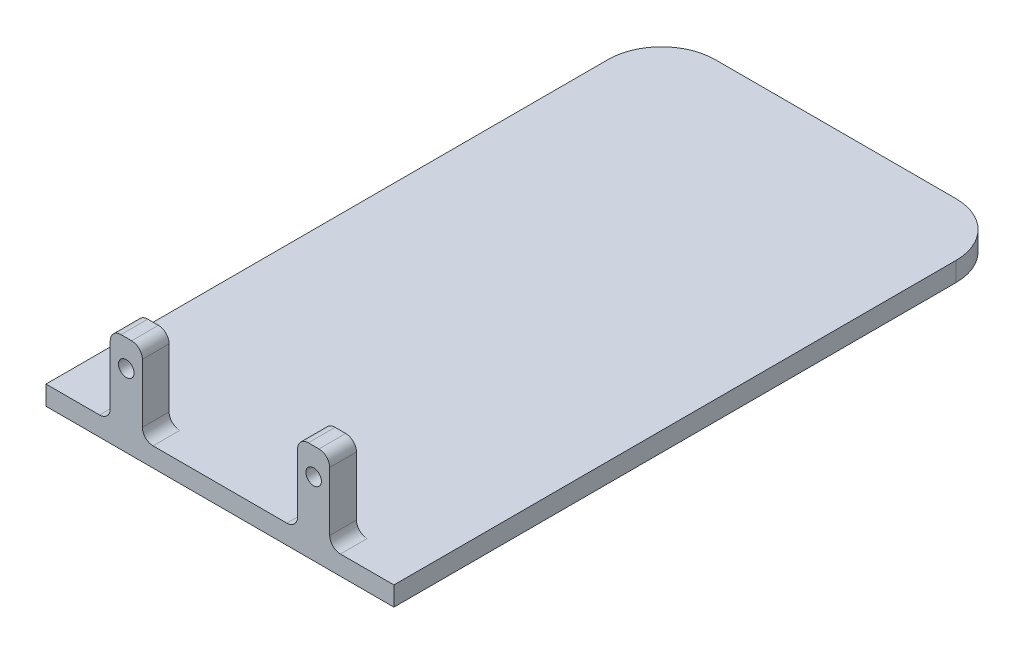
SolidWorks part; units mm, degrees
ref_plane "前视基准面" through (0, 0, 0) normal (0, 0, 1) x (1, 0, 0)
ref_plane "上视基准面" through (0, 0, 0) normal (0, 1, 0) x (1, 0, 0)
ref_plane "右视基准面" through (0, 0, 0) normal (1, 0, 0) x (0, 0, -1)
sketch "草图1" plane through (0, 0, 0) normal (0, 1, 0) x (1, 0, 0)
  line L1 (-38.0503, 26.0407) -> (26.9497, 26.0407)
  line L2 (-38.0503, 26.0407) -> (-38.0503, -88.9593)
  line L3 (-38.0503, -88.9593) -> (26.9497, -88.9593)
  line L4 (26.9497, 26.0407) -> (26.9497, -88.9593)
  dimension "D1" = 65
  dimension "D2" = 115
extrude "凸台-拉伸1" add sketch "草图1" along normal blind 3.6
sketch "草图3" plane through (0, 0, 88.9593) normal (0, 0, 1) x (1, 0, 0)
  line L0 (-5.5503, 3.6) -> (-5.5503, 13.6072) construction
  line L1 (-38.0503, 3.6) -> (26.9497, 3.6) construction
  line L2 (-23.0503, 18.6) -> (-23.0503, 6.8143) construction
  line L3 (-26.0503, 3.6) -> (-20.0503, 3.6)
  line L4 (-26.0503, 3.6) -> (-26.0503, 18.6)
  line L5 (-26.0503, 18.6) -> (-20.0503, 18.6)
  line L6 (-20.0503, 3.6) -> (-20.0503, 18.6)
  line L7 (14.9497, 3.6) -> (8.9497, 3.6)
  line L8 (8.9497, 3.6) -> (8.9497, 18.6)
  line L9 (14.9497, 3.6) -> (14.9497, 18.6)
  line L10 (14.9497, 18.6) -> (8.9497, 18.6)
  circle A0 centre (-23.0503, 13.6) radius 1.45
  circle A1 centre (11.9497, 13.6) radius 1.45
  dimension "D4" = 10
  dimension "D1" = 15
  dimension "D2" = 6
  dimension "D3" = 14.5
extrude "凸台-拉伸2" add sketch "草图3" against normal blind 5
fillet "圆角1" radius 10 2 edges at (26.9497, 1.8, -26.0407) (-38.0503, 1.8, -26.0407)
fillet "圆角2" radius 2 8 edges at (14.9497, 3.6, 86.4593) (-20.0503, 3.6, 86.4593) (8.9497, 3.6, 86.4593) (-26.0503, 3.6, 86.4593) (8.9497, 18.6, 86.4593) (14.9497, 18.6, 86.4593) (-20.0503, 18.6, 86.4593) (-26.0503, 18.6, 86.4593)
